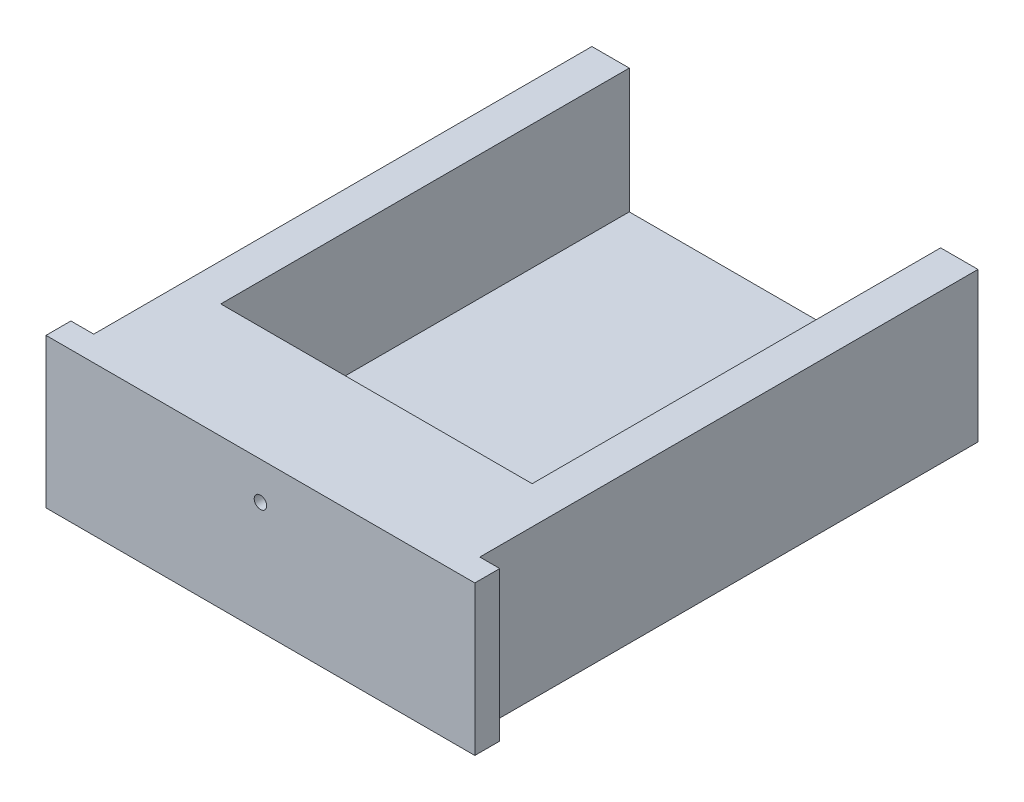
SolidWorks part; units mm, degrees
ref_plane "Front Plane" through (0, 0, 0) normal (0, 0, 1) x (1, 0, 0)
ref_plane "Top Plane" through (0, 0, 0) normal (0, 1, 0) x (1, 0, 0)
ref_plane "Right Plane" through (0, 0, 0) normal (1, 0, 0) x (0, 0, -1)
sketch "Sketch3" plane through (0, 0.0003, -31.967) normal (0, 0, 1) x (1, 0, 0)
  line L0 (106.7306, 145.4577) -> (106.7306, 86.6568) construction
  line L3 (98.9806, 85.6568) -> (114.4806, 85.6568)
  line L5 (98.9807, 206.0576) -> (98.9806, 148.5526) construction
  line L6 (100.4806, 86.6568) -> (112.9806, 86.6568)
  line L7 (114.4807, 206.0576) -> (114.4806, 148.5525) construction
  line L10 (98.9806, 85.6568) -> (98.9806, 91.6568)
  line L11 (98.9806, 91.6568) -> (100.4806, 91.6568)
  line L12 (100.4806, 86.6568) -> (100.4806, 91.6568)
  line L14 (114.4806, 85.6568) -> (114.4806, 91.6568)
  line L15 (114.4806, 91.6568) -> (112.9806, 91.6568)
  line L16 (112.9806, 86.6568) -> (112.9806, 91.6568)
  dimension "D3" = 1
  dimension "D5" = 1.5
  dimension "D6" = 5
extrude "Boss-Extrude1" add sketch "Sketch3" along normal up to surface (20 mm away)
sketch "Sketch4" plane through (0, 0.0001, -11.967) normal (0, 0, 1) x (1, 0, 0)
  line L0 (114.4806, 91.6568) -> (116.0806, 91.6568) construction
  line L1 (98.0647, 91.6568) -> (115.2806, 91.6568)
  line L2 (98.0647, 91.6568) -> (98.0647, 85.6568)
  line L3 (98.0647, 85.6568) -> (115.2806, 85.6568)
  line L4 (115.2806, 91.6568) -> (115.2806, 85.6568)
  line L8 (114.4807, 206.0576) -> (114.4806, 148.5525) construction
  line L14 (116.0807, 206.0576) -> (116.0806, 148.5525) construction
  line L15 (97.3806, 91.6568) -> (98.9806, 91.6568) construction
  line L16 (114.4806, 85.6568) -> (98.9806, 85.6568) construction
  line L17 (97.3807, 206.0576) -> (97.3806, 148.5526) construction
  line L18 (98.9807, 206.0576) -> (98.9806, 148.5526) construction
  line L22 (98.9806, 91.6568) -> (100.4806, 91.6568) construction
extrude "Boss-Extrude2" add sketch "Sketch4" along normal blind 1
sketch "Sketch6" plane through (0, 0.0001, -10.967) normal (0, 0, 1) x (1, 0, 0)
  line L0 (98.0647, 88.6568) -> (115.2806, 88.6568) construction
  line L1 (98.0647, 91.6568) -> (98.0647, 85.6568) construction
  line L2 (115.2806, 85.6568) -> (115.2806, 91.6568) construction
  line L3 (106.6727, 91.6568) -> (106.6727, 85.6568) construction
  line L4 (115.2806, 91.6568) -> (98.0647, 91.6568) construction
  line L5 (98.0647, 85.6568) -> (115.2806, 85.6568) construction
  line L6 (98.0647, 90.1568) -> (115.2806, 90.1568) construction
  line L7 (98.0647, 91.6568) -> (98.0647, 85.6568) construction
  line L8 (115.2806, 85.6568) -> (115.2806, 91.6568) construction
  dimension "D1" = 1.5
sketch "Sketch7" plane through (0, 0.0001, -11.967) normal (0, 0, -1) x (-1, 0, 0)
  line L4 (-112.9806, 91.6568) -> (-112.9806, 86.6568)
  line L5 (-112.9806, 86.6568) -> (-100.4806, 86.6568)
  line L6 (-100.4806, 86.6568) -> (-100.4806, 91.6568)
  line L7 (-100.4806, 91.6568) -> (-112.9806, 91.6568)
  line L8 (-112.9806, 91.6568) -> (-112.9806, 86.6568)
  line L9 (-112.9806, 86.6568) -> (-100.4806, 86.6568)
  line L10 (-100.4806, 86.6568) -> (-100.4806, 91.6568)
  line L11 (-100.4806, 91.6568) -> (-112.9806, 91.6568)
  dimension "D1" = 0
extrude "Boss-Extrude3" add sketch "Sketch7" along normal blind 3.6
sketch "Sketch8" plane through (0, 0.0001, -10.967) normal (0, 0, 1) x (1, 0, 0)
  line L0 (98.0647, 90.1568) -> (115.2806, 90.1568) construction
  point P0 (106.6727, 90.1568)
hole_wizard "Ø1.0mm Dowel Hole1" positions "Sketch10" profile "Sketch11" hole size "Ø1.0" standard "AS" end condition up to next
sketch "Sketch10" plane through (0, 0.0001, -10.967) normal (0, 0, 1) x (1, 0, 0)
  point P0 (106.6727, 90.1568)
sketch "Sketch11" plane through (106.6727, 90.1569, -10.9663) normal (0.7071, 0.7071, 0) x (0.7071, -0.7071, 0)
  line L0 (0, 0) -> (0, 4.6)
  line L1 (0, 4.6) -> (0.25, 4.6)
  line L2 (0.25, 4.6) -> (0.25, 0)
  line L5 (0.25, 0) -> (0, 0)
  line L11 (0, -6.35) -> (0, 107.95) construction
  dimension "Thru Hole Dia." = 0.5
  dimension "Thru Hole Depth" = 4.6
